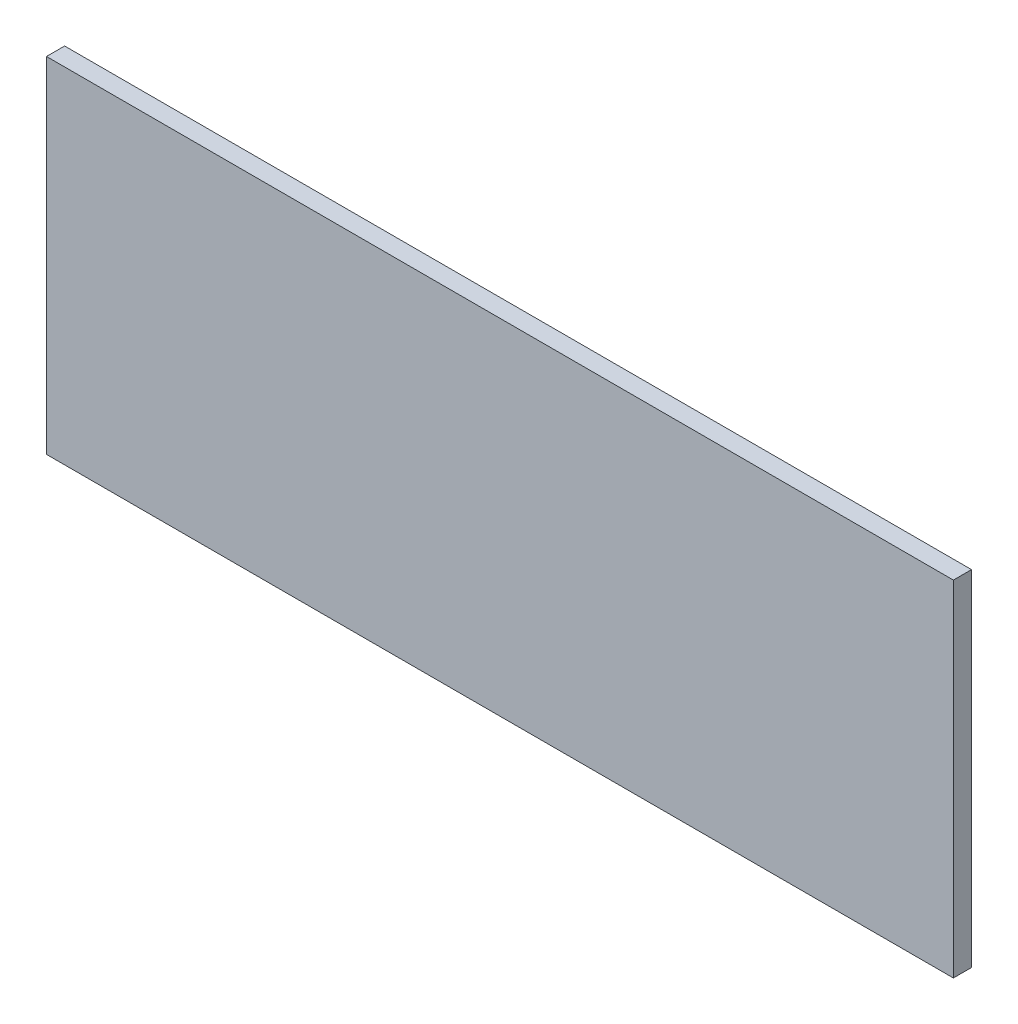
SolidWorks part; units mm, degrees
ref_plane "Plan de face" through (0, 0, 0) normal (0, 0, 1) x (1, 0, 0)
ref_plane "Plan de dessus" through (0, 0, 0) normal (0, 1, 0) x (1, 0, 0)
ref_plane "Plan de droite" through (0, 0, 0) normal (1, 0, 0) x (0, 0, -1)
sketch "Esquisse1" plane through (0, 0, 0) normal (0, 0, 1) x (1, 0, 0)
  line L1 (-68.3146, 26.1581) -> (31.6854, 26.1581)
  line L2 (-68.3146, 26.1581) -> (-68.3146, -11.8419)
  line L3 (-68.3146, -11.8419) -> (31.6854, -11.8419)
  line L4 (31.6854, 26.1581) -> (31.6854, -11.8419)
  dimension "D1" = 38
  dimension "D2" = 100
extrude "Boss.-Extru.1" add sketch "Esquisse1" along normal blind 2
